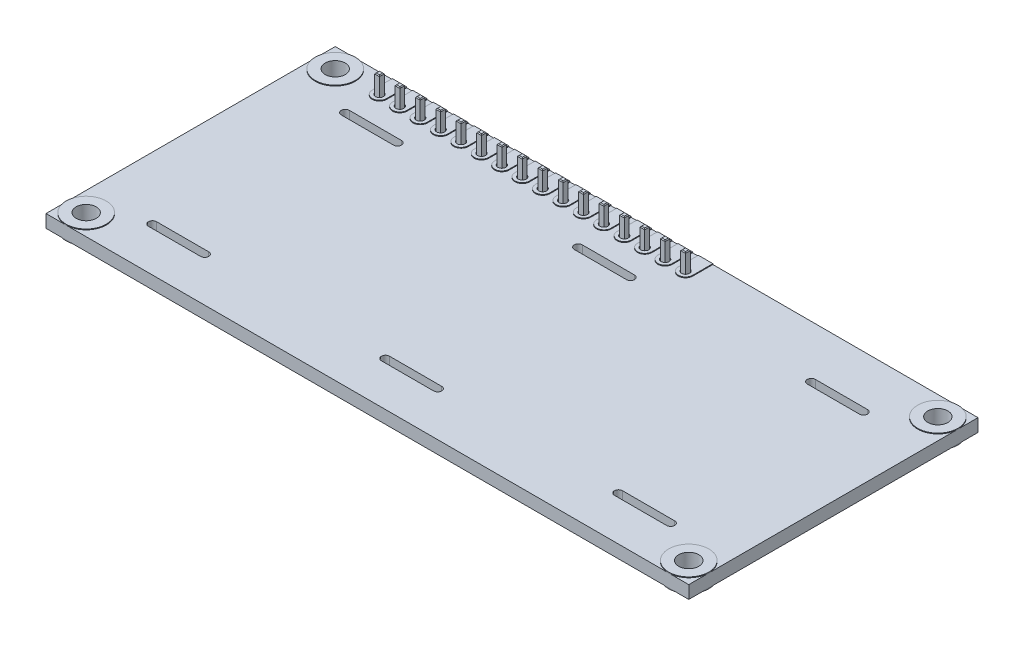
SolidWorks part; units mm, degrees
ref_plane "Front Plane" through (0, 0, 0) normal (0, 0, 1) x (1, 0, 0)
ref_plane "Top Plane" through (0, 0, 0) normal (0, 1, 0) x (1, 0, 0)
ref_plane "Right Plane" through (0, 0, 0) normal (1, 0, 0) x (0, 0, -1)
sketch "Sketch1" plane through (0, 0, 0) normal (0, 1, 0) x (1, 0, 0)
  line L0 (-32, 15.5) -> (-29.46, 15.5) construction
  line L1 (40, 18) -> (-40, 18)
  line L2 (40, 18) -> (40, -18)
  line L3 (40, -18) -> (-40, -18)
  line L4 (-40, 18) -> (-40, -18)
  line L5 (40, 18) -> (-40, -18) construction
  line L6 (40, -18) -> (-40, 18) construction
  line L7 (-37.5, 15.5) -> (37.5, 15.5) construction
  line L8 (-37.5, 15.5) -> (-37.5, -15.5) construction
  line L10 (37.5, 15.5) -> (37.5, -15.5) construction
  line L11 (-37.5, 15.5) -> (37.5, -15.5) construction
  line L12 (-37.5, -15.5) -> (37.5, 15.5) construction
  line L13 (0, 15.5) -> (0, -15.5) construction
  line L14 (-3.25, -12.5) -> (3.25, -12.5) construction
  line L15 (-3.25, -12) -> (3.25, -12)
  line L16 (-3.25, -13) -> (3.25, -13)
  line L17 (25.75, -12.5) -> (32.25, -12.5) construction
  line L18 (25.75, -12) -> (32.25, -12)
  line L19 (25.75, -13) -> (32.25, -13)
  line L20 (25.75, 11.5) -> (32.25, 11.5) construction
  line L21 (25.75, 12) -> (32.25, 12)
  line L22 (25.75, 11) -> (32.25, 11)
  line L23 (-3.25, 11.5) -> (3.25, 11.5) construction
  line L24 (-3.25, 12) -> (3.25, 12)
  line L25 (-3.25, 11) -> (3.25, 11)
  line L26 (-32.25, -12.5) -> (-25.75, -12.5) construction
  line L27 (-32.25, -12) -> (-25.75, -12)
  line L28 (-32.25, -13) -> (-25.75, -13)
  line L29 (-32.25, 11.5) -> (-25.75, 11.5) construction
  line L30 (-32.25, 12) -> (-25.75, 12)
  line L31 (-32.25, 11) -> (-25.75, 11)
  circle A0 centre (-37.5, 15.5) radius 1.25
  circle A1 centre (-37.5, -15.5) radius 1.25
  circle A2 centre (37.5, 15.5) radius 1.25
  circle A3 centre (37.5, -15.5) radius 1.25
  circle A4 centre (-32, 15.5) radius 0.5
  circle A5 centre (-29.46, 15.5) radius 0.5
  circle A6 centre (-26.92, 15.5) radius 0.5
  circle A7 centre (-24.38, 15.5) radius 0.5
  circle A8 centre (-21.84, 15.5) radius 0.5
  circle A9 centre (-19.3, 15.5) radius 0.5
  circle A10 centre (-16.76, 15.5) radius 0.5
  circle A11 centre (-14.22, 15.5) radius 0.5
  circle A12 centre (-11.68, 15.5) radius 0.5
  circle A13 centre (-9.14, 15.5) radius 0.5
  circle A14 centre (-6.6, 15.5) radius 0.5
  circle A15 centre (-4.06, 15.5) radius 0.5
  circle A16 centre (-1.52, 15.5) radius 0.5
  circle A17 centre (1.02, 15.5) radius 0.5
  circle A18 centre (3.56, 15.5) radius 0.5
  circle A19 centre (6.1, 15.5) radius 0.5
  arc A20 (-3.25, -12) -> (-3.25, -13) centre (-3.25, -12.5) ccw
  arc A21 (3.25, -13) -> (3.25, -12) centre (3.25, -12.5) ccw
  arc A22 (25.75, -12) -> (25.75, -13) centre (25.75, -12.5) ccw
  arc A23 (32.25, -13) -> (32.25, -12) centre (32.25, -12.5) ccw
  arc A24 (25.75, 12) -> (25.75, 11) centre (25.75, 11.5) ccw
  arc A25 (32.25, 11) -> (32.25, 12) centre (32.25, 11.5) ccw
  arc A26 (-3.25, 12) -> (-3.25, 11) centre (-3.25, 11.5) ccw
  arc A27 (3.25, 11) -> (3.25, 12) centre (3.25, 11.5) ccw
  arc A28 (-32.25, -12) -> (-32.25, -13) centre (-32.25, -12.5) ccw
  arc A29 (-25.75, -13) -> (-25.75, -12) centre (-25.75, -12.5) ccw
  arc A30 (-32.25, 12) -> (-32.25, 11) centre (-32.25, 11.5) ccw
  arc A31 (-25.75, 11) -> (-25.75, 12) centre (-25.75, 11.5) ccw
  point P0 (0, 0)
  point P6 (0, 0)
  point P51 (-29, 0)
  point P52 (0, -12.5)
  point P55 (0, -12.5)
  point P60 (-29, 0)
  point P62 (29, -12.5)
  point P65 (29, -12.5)
  point P70 (29, 11.5)
  point P73 (29, 11.5)
  point P78 (0, 11.5)
  point P81 (0, 11.5)
  point P86 (-29, -12.5)
  point P89 (-29, -12.5)
  point P94 (-29, 11.5)
  point P97 (-29, 11.5)
  dimension "D5" = 2.5
  dimension "D6" = 1
  dimension "D1" = 36
  dimension "D2" = 80
  dimension "D3" = 2.5
  dimension "D4" = 2.5
  dimension "D7" = 8
  dimension "D9" = 2.54
  dimension "D10" = 1
  dimension "D11" = 6.5
  dimension "D12" = 5
  dimension "D8" = 16
  dimension "D13" = 2
  dimension "D14" = 2
  dimension "D15" = 2
extrude "Boss-Extrude1" add sketch "Sketch1" against normal blind 1.6
sketch "Sketch2" plane through (0, 0, 0) normal (0, 1, 0) x (1, 0, 0)
  line L0 (-32.9, 15.5) -> (-32.9, 18)
  line L1 (40, 18) -> (-40, 18) construction
  line L2 (-32.9, 18) -> (-31.1, 18)
  line L3 (-31.1, 18) -> (-31.1, 15.5)
  arc A0 (-31.1, 15.5) -> (-32.9, 15.5) centre (-32, 15.5) cw
  circle A1 centre (-32, 15.5) radius 0.5 construction
  circle A2 centre (-32, 15.5) radius 0.5
  dimension "D1" = 1.8
extrude "Boss-Extrude2" add sketch "Sketch2" along normal blind 0.1
pattern_linear "LPattern1" count 16 spacing 2.54 along (1, 0, 0) of "Boss-Extrude2"
sketch "Sketch3" plane through (0, 0, 0) normal (0, 1, 0) x (1, 0, 0)
  circle A0 centre (-37.5, 15.5) radius 1.25 construction
  circle A1 centre (-37.5, -15.5) radius 1.25 construction
  circle A2 centre (37.5, 15.5) radius 1.25 construction
  circle A3 centre (37.5, -15.5) radius 1.25 construction
  circle A4 centre (-37.5, 15.5) radius 1.25
  circle A5 centre (-37.5, -15.5) radius 1.25
  circle A6 centre (37.5, 15.5) radius 1.25
  circle A7 centre (37.5, -15.5) radius 1.25
  circle A8 centre (-37.5, 15.5) radius 2.5
  circle A9 centre (-37.5, -15.5) radius 2.5
  circle A10 centre (37.5, -15.5) radius 2.5
  circle A11 centre (37.5, 15.5) radius 2.5
  dimension "D1" = 1.25
extrude "Boss-Extrude3" add sketch "Sketch3" along normal blind 0.1
sketch "Sketch4" plane through (0, -1.6, 0) normal (0, -1, 0) x (1, 0, 0)
  circle A0 centre (37.5, -15.5) radius 1.25 construction
  circle A1 centre (37.5, 15.5) radius 1.25 construction
  circle A2 centre (-37.5, 15.5) radius 1.25 construction
  circle A3 centre (-37.5, -15.5) radius 1.25 construction
  circle A4 centre (37.5, -15.5) radius 1.25
  circle A5 centre (37.5, 15.5) radius 1.25
  circle A6 centre (-37.5, 15.5) radius 1.25
  circle A7 centre (-37.5, -15.5) radius 1.25
  circle A8 centre (37.5, -15.5) radius 2.5
  circle A9 centre (37.5, 15.5) radius 2.5
  circle A10 centre (-37.5, 15.5) radius 2.5
  circle A11 centre (-37.5, -15.5) radius 2.5
  dimension "D1" = 1.25
extrude "Boss-Extrude4" add sketch "Sketch4" along normal blind 0.1
sketch "Sketch5" plane through (0, 0.1, 0) normal (0, 1, 0) x (1, 0, 0)
  line L1 (-32.3, 15.8) -> (-31.7, 15.8)
  line L2 (-32.3, 15.8) -> (-32.3, 15.2)
  line L3 (-32.3, 15.2) -> (-31.7, 15.2)
  line L4 (-31.7, 15.8) -> (-31.7, 15.2)
  line L5 (-32.3, 15.8) -> (-31.7, 15.2) construction
  line L6 (-32.3, 15.2) -> (-31.7, 15.8) construction
  point P0 (-32, 15.5)
  dimension "D1" = 0.6
extrude "Boss-Extrude5" add sketch "Sketch5" along normal blind 2.2 and the other way blind 9.9 separate body
sketch "Sketch6" plane through (0, 2.3, 0) normal (0, 1, 0) x (1, 0, 0)
  line L0 (-32.3, 15.8) -> (-32.3, 15.2) construction
  line L1 (-32.3, 15.2) -> (-31.7, 15.2) construction
  line L2 (-31.7, 15.2) -> (-31.7, 15.8) construction
  line L3 (-31.7, 15.8) -> (-32.3, 15.8) construction
  line L4 (-32.3, 15.8) -> (-32.3, 15.2)
  line L5 (-32.3, 15.2) -> (-31.7, 15.2)
  line L6 (-31.7, 15.2) -> (-31.7, 15.8)
  line L7 (-31.7, 15.8) -> (-32.3, 15.8)
extrude "Boss-Extrude6" add sketch "Sketch6" along normal blind 0.1 draft 45
sketch "Sketch7" plane through (0, -9.8, 0) normal (0, -1, 0) x (1, 0, 0)
  line L0 (-32.3, -15.2) -> (-31.7, -15.2) construction
  line L1 (-31.7, -15.2) -> (-31.7, -15.8) construction
  line L2 (-31.7, -15.8) -> (-32.3, -15.8) construction
  line L3 (-32.3, -15.8) -> (-32.3, -15.2) construction
  line L4 (-32.3, -15.2) -> (-31.7, -15.2)
  line L5 (-31.7, -15.2) -> (-31.7, -15.8)
  line L6 (-31.7, -15.8) -> (-32.3, -15.8)
  line L7 (-32.3, -15.8) -> (-32.3, -15.2)
extrude "Boss-Extrude7" add sketch "Sketch7" along normal blind 0.1 draft 45
pattern_linear "LPattern2" count 16 spacing 2.54 along (1, 0, 0) of "Boss-Extrude5", "Boss-Extrude6", "Boss-Extrude7"
sketch "Sketch8" plane through (0, -1.6, 0) normal (0, -1, 0) x (1, 0, 0)
  line L1 (-33.25, -14.25) -> (7.25, -14.25)
  line L2 (-33.25, -14.25) -> (-33.25, -16.75)
  line L3 (-33.25, -16.75) -> (7.25, -16.75)
  line L4 (7.25, -14.25) -> (7.25, -16.75)
  circle A0 centre (-32, -15.5) radius 0.5 construction
  dimension "D4" = 1.25
  dimension "D1" = 2.5
  dimension "D2" = 40.5
  dimension "D3" = 1.25
extrude "Boss-Extrude8" add sketch "Sketch8" along normal blind 2.5
